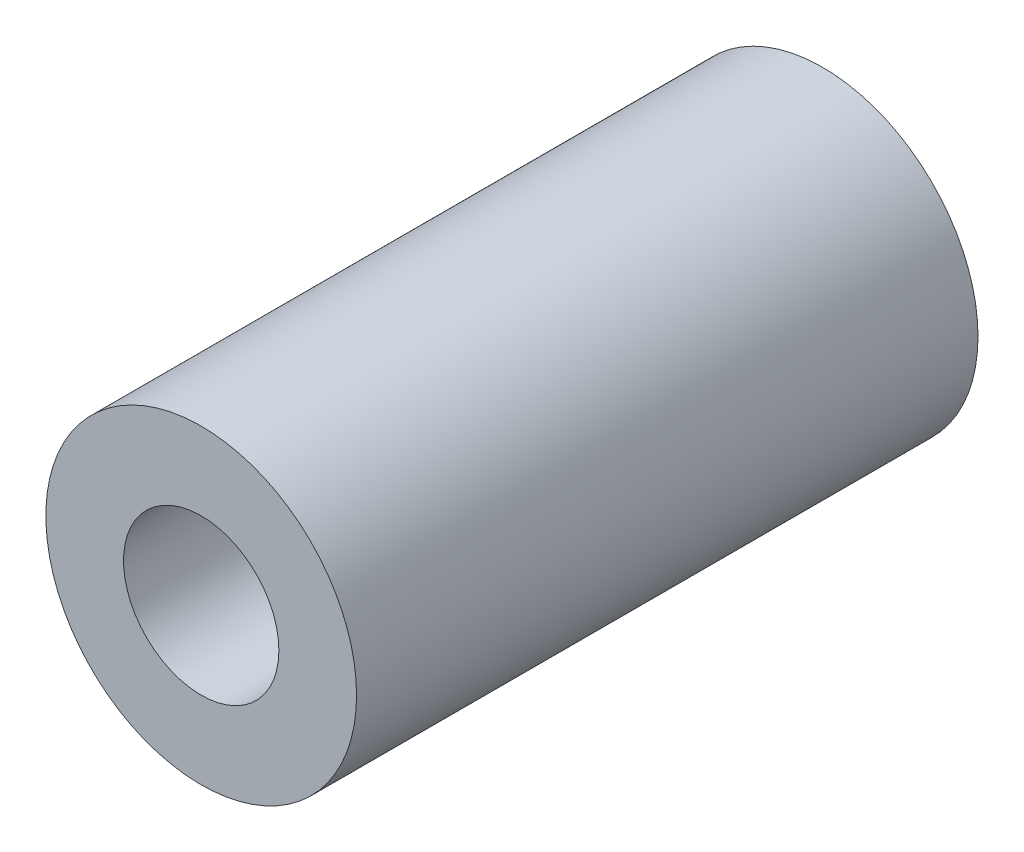
SolidWorks part; units mm, degrees
material "Aluminum Bronze"
ref_plane "Front Plane" through (0, 0, 0) normal (0, 0, 1) x (1, 0, 0)
ref_plane "Top Plane" through (0, 0, 0) normal (0, 1, 0) x (1, 0, 0)
ref_plane "Right Plane" through (0, 0, 0) normal (1, 0, 0) x (0, 0, -1)
sketch "Sketch1" plane through (0, 0, 0) normal (0, 0, 1) x (1, 0, 0)
  circle A0 centre (0, 0) radius 3.175
  circle A1 centre (0, 0) radius 1.5875
  dimension "D1" = 6.35
  dimension "D2" = 3.175
extrude "Boss-Extrude1" add sketch "Sketch1" along normal blind 12.7
